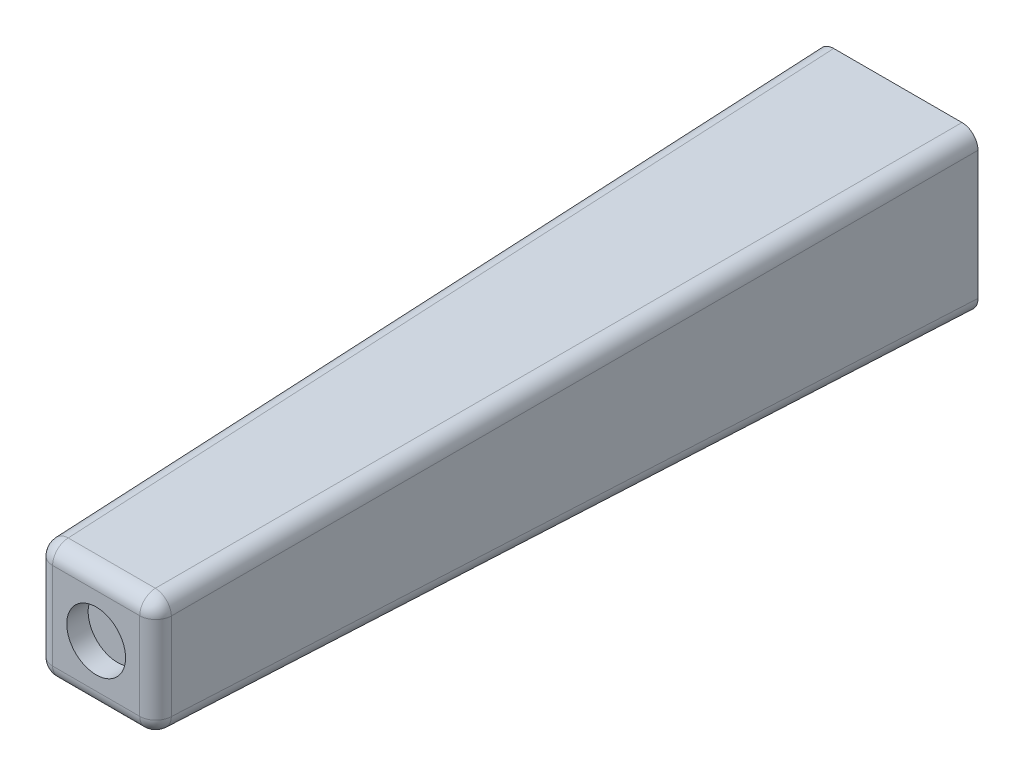
SolidWorks part; units mm, degrees
ref_plane "Спереди" through (0, 0, 0) normal (0, 0, 1) x (1, 0, 0)
ref_plane "Сверху" through (0, 0, 0) normal (0, 1, 0) x (1, 0, 0)
ref_plane "Справа" through (0, 0, 0) normal (1, 0, 0) x (0, 0, -1)
other "Configuration Table"
sketch "Sketch1" plane through (0, 0, 0) normal (0, 0, 1) x (1, 0, 0)
  line L1 (-7.5, -7.5) -> (7.5, -7.5)
  line L2 (-7.5, -7.5) -> (-7.5, 7.5)
  line L3 (-7.5, 7.5) -> (7.5, 7.5)
  line L4 (7.5, -7.5) -> (7.5, 7.5)
  line L5 (-7.5, -7.5) -> (7.5, 7.5) construction
  line L6 (-7.5, 7.5) -> (7.5, -7.5) construction
  point P0 (0, 0)
  dimension "D1" = 15
  dimension "D2" = 15
extrude "Boss-Extrude1" add sketch "Sketch1" along normal blind 75 draft 1.5
sketch "Sketch2" plane through (0, 0, 0) normal (0, 0, -1) x (-1, 0, 0)
  circle A0 centre (0, 0) radius 1.5
  dimension "D1" = 3
extrude "Cut-Extrude1" cut sketch "Sketch2" against normal blind 10
sketch "Sketch3" plane through (0, 0, 75) normal (0, 0, 1) x (1, 0, 0)
  circle A0 centre (0, 0) radius 2.75
  dimension "D1" = 5.5
extrude "Cut-Extrude2" cut sketch "Sketch3" against normal blind 2
fillet "Fillet1" radius 1.5 8 edges at (0, 5.5361, 75) (5.5361, 0, 75) (0, -5.5361, 75) (-5.5361, 0, 75) (-6.518, -6.518, 37.5) (6.518, 6.518, 37.5) (-6.518, 6.518, 37.5) (6.518, -6.518, 37.5)
fillet "Fillet2" radius 0.5 1 edges at (-1.5, 0, 0)
